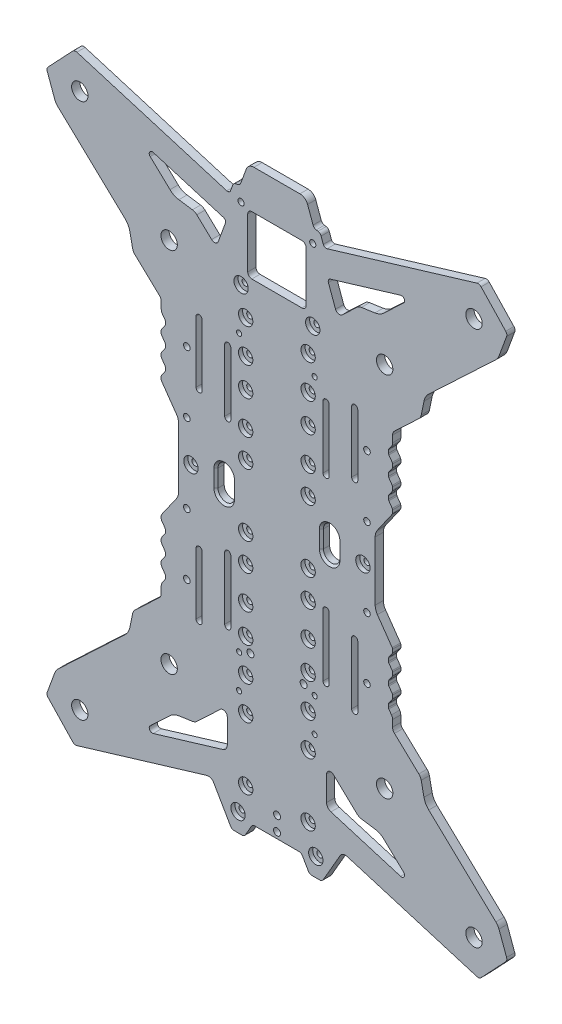
SolidWorks part; units mm, degrees
ref_plane "Front Plane" through (0, 0, 0) normal (0, 0, 1) x (1, 0, 0)
ref_plane "Top Plane" through (0, 0, 0) normal (0, 1, 0) x (1, 0, 0)
ref_plane "Right Plane" through (0, 0, 0) normal (1, 0, 0) x (0, 0, -1)
sketch "Model" plane through (0, 0, 0) normal (0, 0, 1) x (1, 0, 0)
  line L0 (183.8108, 197.417) -> (183.8108, 227.917)
  line L1 (186.8108, 227.917) -> (186.8108, 197.417)
  line L2 (138.8108, 139.917) -> (138.8108, 109.417)
  line L3 (135.8108, 109.417) -> (135.8108, 139.917)
  line L4 (186.8108, 139.917) -> (186.8108, 109.417)
  line L5 (183.8108, 109.417) -> (183.8108, 139.917)
  line L6 (135.8108, 197.417) -> (135.8108, 227.917)
  line L7 (138.8108, 227.917) -> (138.8108, 197.417)
  line L8 (147.0608, 264.0945) -> (147.0608, 288.5945)
  line L9 (173.5608, 262.0945) -> (149.0608, 262.0945)
  line L10 (175.5608, 288.5945) -> (175.5608, 264.0945)
  line L11 (149.0608, 290.5945) -> (173.5608, 290.5945)
  line L12 (133.6884, 72.3677) -> (122.1935, 61.5247)
  line L13 (120.0282, 60.4766) -> (113.4215, 59.5095)
  line L14 (100.8847, 45.7661) -> (134.926, 56.02)
  line L15 (209.2, 59.5095) -> (202.5933, 60.4766)
  line L16 (200.428, 61.5247) -> (188.9331, 72.3677)
  line L17 (185.5608, 58.8925) -> (185.5608, 70.9128)
  line L18 (187.6955, 56.02) -> (221.7368, 45.7661)
  line L19 (223.1987, 48.2935) -> (213.5306, 57.4133)
  line L20 (113.4215, 277.8244) -> (120.0282, 276.8573)
  line L21 (122.1935, 275.8092) -> (129.4288, 268.9842)
  line L22 (135.174, 281.2392) -> (100.8847, 291.5678)
  line L23 (99.4228, 289.0404) -> (109.0909, 279.9206)
  line L24 (261.0344, 314.783) -> (273.0616, 302.0327)
  line L25 (273.4849, 299.9728) -> (269.7846, 289.8648)
  line L26 (268.2674, 287.5628) -> (235.4884, 256.6428)
  line L27 (233.1432, 252.4417) -> (231.7925, 245.9027)
  line L28 (230.6199, 243.8022) -> (218.7522, 232.6075)
  line L29 (217.8108, 230.4252) -> (217.8108, 227.2161)
  line L30 (217.2682, 225.4954) -> (215.9916, 223.6722)
  line L31 (215.8108, 223.0986) -> (215.8108, 221.7292)
  line L32 (215.9916, 221.1557) -> (217.6299, 218.8159)
  line L33 (217.8108, 218.2423) -> (217.8108, 216.8729)
  line L34 (217.6299, 216.2994) -> (215.9916, 213.9596)
  line L35 (215.8108, 213.386) -> (215.8108, 212.0166)
  line L36 (215.9916, 211.4431) -> (217.6299, 209.1033)
  line L37 (217.8108, 208.5298) -> (217.8108, 207.1603)
  line L38 (217.6299, 206.5868) -> (215.9916, 204.247)
  line L39 (215.8108, 203.6735) -> (215.8108, 202.304)
  line L40 (215.9916, 201.7305) -> (217.6299, 199.3907)
  line L41 (217.8108, 198.8172) -> (217.8108, 197.4478)
  line L42 (217.6299, 196.8742) -> (210.3959, 186.5429)
  line L43 (209.3108, 183.1014) -> (209.3108, 154.2325)
  line L44 (210.3959, 150.791) -> (217.6299, 140.4597)
  line L45 (217.8108, 139.8861) -> (217.8108, 138.5167)
  line L46 (217.6299, 137.9432) -> (215.9916, 135.6034)
  line L47 (215.8108, 135.0299) -> (215.8108, 133.6605)
  line L48 (215.9916, 133.0869) -> (217.6299, 130.7471)
  line L49 (217.8108, 130.1736) -> (217.8108, 128.8042)
  line L50 (217.6299, 128.2306) -> (215.9916, 125.8908)
  line L51 (215.8108, 125.3173) -> (215.8108, 123.9479)
  line L52 (215.9916, 123.3743) -> (217.6299, 121.0345)
  line L53 (217.8108, 120.461) -> (217.8108, 119.0916)
  line L54 (217.6299, 118.518) -> (215.9916, 116.1782)
  line L55 (215.8108, 115.6047) -> (215.8108, 114.2353)
  line L56 (215.9916, 113.6617) -> (217.2682, 111.8385)
  line L57 (217.8108, 110.1178) -> (217.8108, 106.9087)
  line L58 (218.7522, 104.7264) -> (230.6199, 93.5317)
  line L59 (231.7925, 91.4312) -> (233.1432, 84.8922)
  line L60 (235.4884, 80.6911) -> (268.2674, 49.7711)
  line L61 (269.7846, 47.4691) -> (273.4849, 37.3611)
  line L62 (273.0616, 35.3012) -> (261.0344, 22.5509)
  line L63 (259.0027, 22.0083) -> (195.64, 41.0944)
  line L64 (192.1766, 39.7219) -> (183.942, 25.4591)
  line L65 (182.2099, 24.4591) -> (178.4116, 24.4591)
  line L66 (176.6796, 25.4591) -> (173.7928, 30.4591)
  line L67 (172.0608, 31.4591) -> (150.5608, 31.4591)
  line L68 (148.8287, 30.4591) -> (145.942, 25.4591)
  line L69 (144.2099, 24.4591) -> (140.4116, 24.4591)
  line L70 (138.6796, 25.4591) -> (130.4449, 39.7219)
  line L71 (126.9816, 41.0944) -> (63.6188, 22.0083)
  line L72 (61.5871, 22.5509) -> (49.5599, 35.3012)
  line L73 (49.1366, 37.3611) -> (52.8369, 47.4691)
  line L74 (54.3542, 49.7711) -> (87.1331, 80.6911)
  line L75 (89.4783, 84.8922) -> (90.8291, 91.4312)
  line L76 (92.0016, 93.5317) -> (103.8693, 104.7264)
  line L77 (104.8108, 106.9087) -> (104.8108, 110.1178)
  line L78 (105.3533, 111.8385) -> (106.6299, 113.6617)
  line L79 (106.8108, 114.2353) -> (106.8108, 115.6047)
  line L80 (106.6299, 116.1782) -> (104.9916, 118.518)
  line L81 (104.8108, 119.0916) -> (104.8108, 120.461)
  line L82 (104.9916, 121.0345) -> (106.6299, 123.3743)
  line L83 (106.6299, 125.8908) -> (104.9916, 128.2306)
  line L84 (104.8108, 128.8042) -> (104.8108, 130.1736)
  line L85 (104.9916, 130.7471) -> (106.6299, 133.0869)
  line L86 (106.8108, 133.6605) -> (106.8108, 135.0299)
  line L87 (106.6299, 135.6034) -> (104.9916, 137.9432)
  line L88 (104.8108, 138.5167) -> (104.8108, 139.8861)
  line L89 (104.9916, 140.4597) -> (112.2257, 150.791)
  line L90 (113.3108, 154.2325) -> (113.3108, 183.1014)
  line L91 (112.2257, 186.5429) -> (104.9916, 196.8742)
  line L92 (104.8108, 197.4478) -> (104.8108, 198.8172)
  line L93 (104.9916, 199.3907) -> (106.6299, 201.7305)
  line L94 (106.8108, 202.304) -> (106.8108, 203.6735)
  line L95 (106.6299, 204.247) -> (104.9916, 206.5868)
  line L96 (104.8108, 207.1603) -> (104.8108, 208.5298)
  line L97 (104.9916, 209.1033) -> (106.6299, 211.4431)
  line L98 (106.8108, 212.0166) -> (106.8108, 213.386)
  line L99 (106.6299, 213.9596) -> (104.9916, 216.2994)
  line L100 (104.8108, 216.8729) -> (104.8108, 218.2423)
  line L101 (104.9916, 218.8159) -> (106.6299, 221.1557)
  line L102 (106.8108, 221.7292) -> (106.8108, 223.0986)
  line L103 (106.6299, 223.6722) -> (105.3533, 225.4954)
  line L104 (104.8108, 227.2161) -> (104.8108, 230.4252)
  line L105 (103.8693, 232.6075) -> (92.0016, 243.8022)
  line L106 (90.8291, 245.9027) -> (89.4783, 252.4417)
  line L107 (87.1331, 256.6428) -> (54.3542, 287.5628)
  line L108 (52.8369, 289.8648) -> (49.1366, 299.9728)
  line L109 (49.5599, 302.0327) -> (61.5871, 314.783)
  line L110 (63.6188, 315.3256) -> (136.8099, 293.279)
  line L111 (138.6521, 294.2022) -> (139.728, 297.1583)
  line L112 (141.2601, 298.4439) -> (142.113, 298.5943)
  line L113 (143.6451, 299.8798) -> (146.325, 307.2429)
  line L114 (150.0838, 309.8748) -> (172.5378, 309.8748)
  line L115 (176.2965, 307.2429) -> (178.9765, 299.8798)
  line L116 (180.5086, 298.5943) -> (181.3614, 298.4439)
  line L117 (185.8116, 293.279) -> (259.0027, 315.3256)
  line L118 (193.1927, 268.9842) -> (200.428, 275.8092)
  line L119 (202.5933, 276.8573) -> (209.2, 277.8244)
  line L120 (221.7368, 291.5678) -> (187.4475, 281.2392)
  line L121 (186.4706, 279.2899) -> (189.941, 269.7551)
  line L122 (106.8108, 123.9479) -> (106.8108, 125.3173)
  line L123 (137.0608, 70.9128) -> (137.0608, 58.8925)
  line L124 (109.0909, 57.4133) -> (99.4228, 48.2935)
  line L125 (132.6805, 269.7551) -> (136.1509, 279.2899)
  line L126 (182.8935, 297.1583) -> (183.9694, 294.2022)
  line L127 (213.5306, 279.9206) -> (223.1987, 289.0404)
  circle A0 centre (178.8108, 292.022) radius 1.5
  arc A1 (183.8108, 197.417) -> (186.8108, 197.417) centre (185.3108, 197.417) ccw
  arc A2 (186.8108, 227.917) -> (183.8108, 227.917) centre (185.3108, 227.917) ccw
  arc A3 (138.8108, 139.917) -> (135.8108, 139.917) centre (137.3108, 139.917) ccw
  arc A4 (135.8108, 109.417) -> (138.8108, 109.417) centre (137.3108, 109.417) ccw
  circle A5 centre (213.9455, 258.3167) radius 4
  circle A6 centre (257.5914, 299.4875) radius 4
  circle A7 centre (65.0301, 299.4875) radius 4
  circle A8 centre (108.6761, 258.3167) radius 4
  circle A9 centre (108.6761, 79.0172) radius 4
  circle A10 centre (65.0301, 37.8464) radius 4
  circle A11 centre (257.5914, 37.8464) radius 4
  circle A12 centre (213.9455, 79.0172) radius 4
  arc A13 (186.8108, 139.917) -> (183.8108, 139.917) centre (185.3108, 139.917) ccw
  arc A14 (183.8108, 109.417) -> (186.8108, 109.417) centre (185.3108, 109.417) ccw
  arc A15 (135.8108, 197.417) -> (138.8108, 197.417) centre (137.3108, 197.417) ccw
  arc A16 (138.8108, 227.917) -> (135.8108, 227.917) centre (137.3108, 227.917) ccw
  circle A17 centre (143.8108, 292.022) radius 1.5
  arc A18 (147.0608, 264.0945) -> (149.0608, 262.0945) centre (149.0608, 264.0945) ccw
  arc A19 (173.5608, 262.0945) -> (175.5608, 264.0945) centre (173.5608, 264.0945) ccw
  arc A20 (175.5608, 288.5945) -> (173.5608, 290.5945) centre (173.5608, 288.5945) ccw
  arc A21 (149.0608, 290.5945) -> (147.0608, 288.5945) centre (149.0608, 288.5945) ccw
  circle A22 centre (146.0608, 227.917) radius 3.5 construction
  circle A23 centre (176.5608, 227.917) radius 3.5 construction
  circle A24 centre (176.5608, 197.417) radius 3.5 construction
  circle A25 centre (146.0608, 197.417) radius 3.5 construction
  circle A26 centre (119.3108, 168.667) radius 3.5 construction
  circle A27 centre (203.3108, 168.667) radius 3.5 construction
  circle A28 centre (146.0608, 183.917) radius 3.5 construction
  circle A29 centre (176.5608, 183.917) radius 3.5 construction
  circle A30 centre (146.0608, 153.417) radius 3.5 construction
  circle A31 centre (176.5608, 153.417) radius 3.5 construction
  circle A32 centre (146.0608, 139.917) radius 3.5 construction
  circle A33 centre (176.5608, 139.917) radius 3.5 construction
  circle A34 centre (146.0608, 109.417) radius 3.5 construction
  circle A35 centre (176.5608, 109.417) radius 3.5 construction
  circle A36 centre (146.0608, 76.667) radius 3.5 construction
  circle A37 centre (176.5608, 76.667) radius 3.5 construction
  circle A38 centre (146.0608, 46.167) radius 3.5 construction
  circle A39 centre (176.5608, 46.167) radius 3.5 construction
  circle A40 centre (142.3108, 33.4591) radius 3.5 construction
  circle A41 centre (180.3108, 33.4591) radius 3.5 construction
  circle A42 centre (176.5608, 93.042) radius 3.5 construction
  circle A43 centre (146.0608, 93.042) radius 3.5 construction
  circle A44 centre (176.5608, 123.542) radius 3.5 construction
  circle A45 centre (146.0608, 123.542) radius 3.5 construction
  circle A46 centre (176.5608, 213.792) radius 3.5 construction
  circle A47 centre (146.0608, 213.792) radius 3.5 construction
  circle A48 centre (176.5608, 244.292) radius 3.5 construction
  circle A49 centre (146.0608, 244.292) radius 3.5 construction
  circle A50 centre (178.8108, 257.022) radius 3.5 construction
  circle A51 centre (143.8108, 257.022) radius 3.5 construction
  arc A52 (137.0608, 70.9128) -> (133.6884, 72.3677) centre (135.0608, 70.9128) ccw
  arc A53 (120.0282, 60.4766) -> (122.1935, 61.5247) centre (119.4488, 64.4344) ccw
  arc A54 (113.4215, 59.5095) -> (109.0909, 57.4133) centre (114.5803, 51.5938) ccw
  arc A55 (99.4228, 48.2935) -> (100.8847, 45.7661) centre (100.4521, 47.2023) ccw
  arc A56 (134.926, 56.02) -> (137.0608, 58.8925) centre (134.0608, 58.8925) ccw
  arc A57 (200.428, 61.5247) -> (202.5933, 60.4766) centre (203.1727, 64.4344) ccw
  arc A58 (188.9331, 72.3677) -> (185.5608, 70.9128) centre (187.5608, 70.9128) ccw
  arc A59 (185.5608, 58.8925) -> (187.6955, 56.02) centre (188.5608, 58.8925) ccw
  arc A60 (221.7368, 45.7661) -> (223.1987, 48.2935) centre (222.1695, 47.2023) ccw
  arc A61 (213.5306, 57.4133) -> (209.2, 59.5095) centre (208.0412, 51.5938) ccw
  arc A62 (122.1935, 275.8092) -> (120.0282, 276.8573) centre (119.4488, 272.8995) ccw
  arc A63 (129.4288, 268.9842) -> (132.6805, 269.7551) centre (130.8012, 270.4391) ccw
  arc A64 (136.1509, 279.2899) -> (135.174, 281.2392) centre (134.7414, 279.8029) ccw
  arc A65 (100.8847, 291.5678) -> (99.4228, 289.0404) centre (100.4521, 290.1316) ccw
  arc A66 (109.0909, 279.9206) -> (113.4215, 277.8244) centre (114.5803, 285.7401) ccw
  arc A67 (261.0344, 314.783) -> (259.0027, 315.3256) centre (259.5795, 313.4106) ccw
  arc A68 (273.4849, 299.9728) -> (273.0616, 302.0327) centre (271.6068, 300.6603) ccw
  arc A69 (268.2674, 287.5628) -> (269.7846, 289.8648) centre (264.1503, 291.9274) ccw
  arc A70 (235.4884, 256.6428) -> (233.1432, 252.4417) centre (240.9778, 250.8233) ccw
  arc A71 (230.6199, 243.8022) -> (231.7925, 245.9027) centre (227.8752, 246.7119) ccw
  arc A72 (218.7522, 232.6075) -> (217.8108, 230.4252) centre (220.8108, 230.4252) ccw
  arc A73 (217.2682, 225.4954) -> (217.8108, 227.2161) centre (214.8108, 227.2161) ccw
  arc A74 (215.9916, 223.6722) -> (215.8108, 223.0986) centre (216.8108, 223.0986) ccw
  arc A75 (215.8108, 221.7292) -> (215.9916, 221.1557) centre (216.8108, 221.7292) ccw
  arc A76 (217.8108, 218.2423) -> (217.6299, 218.8159) centre (216.8108, 218.2423) ccw
  arc A77 (217.6299, 216.2994) -> (217.8108, 216.8729) centre (216.8108, 216.8729) ccw
  arc A78 (215.9916, 213.9596) -> (215.8108, 213.386) centre (216.8108, 213.386) ccw
  arc A79 (215.8108, 212.0166) -> (215.9916, 211.4431) centre (216.8108, 212.0166) ccw
  arc A80 (217.8108, 208.5298) -> (217.6299, 209.1033) centre (216.8108, 208.5298) ccw
  arc A81 (217.6299, 206.5868) -> (217.8108, 207.1603) centre (216.8108, 207.1603) ccw
  arc A82 (215.9916, 204.247) -> (215.8108, 203.6735) centre (216.8108, 203.6735) ccw
  arc A83 (215.8108, 202.304) -> (215.9916, 201.7305) centre (216.8108, 202.3041) ccw
  arc A84 (217.8108, 198.8172) -> (217.6299, 199.3907) centre (216.8108, 198.8172) ccw
  arc A85 (217.6299, 196.8742) -> (217.8108, 197.4478) centre (216.8108, 197.4478) ccw
  arc A86 (210.3959, 186.5429) -> (209.3108, 183.1014) centre (215.3108, 183.1014) ccw
  arc A87 (209.3108, 154.2325) -> (210.3959, 150.791) centre (215.3108, 154.2325) ccw
  arc A88 (217.8108, 139.8861) -> (217.6299, 140.4597) centre (216.8108, 139.8861) ccw
  arc A89 (217.6299, 137.9432) -> (217.8108, 138.5167) centre (216.8108, 138.5167) ccw
  arc A90 (215.9916, 135.6034) -> (215.8108, 135.0299) centre (216.8108, 135.0299) ccw
  arc A91 (215.8108, 133.6605) -> (215.9916, 133.0869) centre (216.8108, 133.6604) ccw
  arc A92 (217.8108, 130.1736) -> (217.6299, 130.7471) centre (216.8108, 130.1736) ccw
  arc A93 (217.6299, 128.2306) -> (217.8108, 128.8042) centre (216.8108, 128.8042) ccw
  arc A94 (215.9916, 125.8908) -> (215.8108, 125.3173) centre (216.8108, 125.3173) ccw
  arc A95 (215.8108, 123.9479) -> (215.9916, 123.3743) centre (216.8108, 123.9479) ccw
  arc A96 (217.8108, 120.461) -> (217.6299, 121.0345) centre (216.8108, 120.461) ccw
  arc A97 (217.6299, 118.518) -> (217.8108, 119.0916) centre (216.8108, 119.0916) ccw
  arc A98 (215.9916, 116.1782) -> (215.8108, 115.6047) centre (216.8108, 115.6047) ccw
  arc A99 (215.8108, 114.2353) -> (215.9916, 113.6617) centre (216.8108, 114.2353) ccw
  arc A100 (217.8108, 110.1178) -> (217.2682, 111.8385) centre (214.8108, 110.1178) ccw
  arc A101 (217.8108, 106.9087) -> (218.7522, 104.7264) centre (220.8108, 106.9087) ccw
  arc A102 (231.7925, 91.4312) -> (230.6199, 93.5317) centre (227.8752, 90.622) ccw
  arc A103 (233.1432, 84.8922) -> (235.4884, 80.6911) centre (240.9778, 86.5106) ccw
  arc A104 (269.7846, 47.4691) -> (268.2674, 49.7711) centre (264.1503, 45.4065) ccw
  arc A105 (273.0616, 35.3012) -> (273.4849, 37.3611) centre (271.6068, 36.6736) ccw
  arc A106 (259.0027, 22.0083) -> (261.0344, 22.5509) centre (259.5795, 23.9233) ccw
  arc A107 (195.64, 41.0944) -> (192.1766, 39.7219) centre (194.7747, 38.2219) ccw
  arc A108 (182.2099, 24.4591) -> (183.942, 25.4591) centre (182.2099, 26.4591) ccw
  arc A109 (176.6796, 25.4591) -> (178.4116, 24.4591) centre (178.4116, 26.4591) ccw
  arc A110 (173.7928, 30.4591) -> (172.0608, 31.4591) centre (172.0608, 29.4591) ccw
  arc A111 (150.5608, 31.4591) -> (148.8287, 30.4591) centre (150.5608, 29.4591) ccw
  arc A112 (144.2099, 24.4591) -> (145.942, 25.4591) centre (144.2099, 26.4591) ccw
  arc A113 (138.6796, 25.4591) -> (140.4116, 24.4591) centre (140.4116, 26.4591) ccw
  arc A114 (130.4449, 39.7219) -> (126.9816, 41.0944) centre (127.8468, 38.2219) ccw
  arc A115 (61.5871, 22.5509) -> (63.6188, 22.0083) centre (63.042, 23.9233) ccw
  arc A116 (49.1366, 37.3611) -> (49.5599, 35.3012) centre (51.0147, 36.6736) ccw
  arc A117 (54.3542, 49.7711) -> (52.8369, 47.4691) centre (58.4712, 45.4065) ccw
  arc A118 (87.1331, 80.6911) -> (89.4783, 84.8922) centre (81.6437, 86.5106) ccw
  arc A119 (92.0016, 93.5317) -> (90.8291, 91.4312) centre (94.7464, 90.622) ccw
  arc A120 (103.8693, 104.7264) -> (104.8108, 106.9087) centre (101.8108, 106.9087) ccw
  arc A121 (105.3533, 111.8385) -> (104.8108, 110.1178) centre (107.8108, 110.1178) ccw
  arc A122 (106.6299, 113.6617) -> (106.8108, 114.2353) centre (105.8108, 114.2353) ccw
  arc A123 (106.8108, 115.6047) -> (106.6299, 116.1782) centre (105.8108, 115.6047) ccw
  arc A124 (104.8108, 119.0916) -> (104.9916, 118.518) centre (105.8108, 119.0916) ccw
  arc A125 (104.9916, 121.0345) -> (104.8108, 120.461) centre (105.8108, 120.461) ccw
  arc A126 (106.6299, 123.3743) -> (106.8108, 123.9479) centre (105.8108, 123.9479) ccw
  arc A127 (106.8108, 125.3173) -> (106.6299, 125.8908) centre (105.8108, 125.3173) ccw
  arc A128 (104.8108, 128.8042) -> (104.9916, 128.2306) centre (105.8108, 128.8042) ccw
  arc A129 (104.9916, 130.7471) -> (104.8108, 130.1736) centre (105.8108, 130.1736) ccw
  arc A130 (106.6299, 133.0869) -> (106.8108, 133.6605) centre (105.8108, 133.6604) ccw
  arc A131 (106.8108, 135.0299) -> (106.6299, 135.6034) centre (105.8108, 135.0299) ccw
  arc A132 (104.8108, 138.5167) -> (104.9916, 137.9432) centre (105.8108, 138.5167) ccw
  arc A133 (104.9916, 140.4597) -> (104.8108, 139.8861) centre (105.8108, 139.8861) ccw
  arc A134 (112.2257, 150.791) -> (113.3108, 154.2325) centre (107.3108, 154.2325) ccw
  arc A135 (113.3108, 183.1014) -> (112.2257, 186.5429) centre (107.3108, 183.1014) ccw
  arc A136 (104.8108, 197.4478) -> (104.9916, 196.8742) centre (105.8108, 197.4478) ccw
  arc A137 (104.9916, 199.3907) -> (104.8108, 198.8172) centre (105.8108, 198.8172) ccw
  arc A138 (106.6299, 201.7305) -> (106.8108, 202.304) centre (105.8108, 202.3041) ccw
  arc A139 (106.8108, 203.6735) -> (106.6299, 204.247) centre (105.8108, 203.6735) ccw
  arc A140 (104.8108, 207.1603) -> (104.9916, 206.5868) centre (105.8108, 207.1603) ccw
  arc A141 (104.9916, 209.1033) -> (104.8108, 208.5298) centre (105.8108, 208.5298) ccw
  arc A142 (106.6299, 211.4431) -> (106.8108, 212.0166) centre (105.8108, 212.0166) ccw
  arc A143 (106.8108, 213.386) -> (106.6299, 213.9596) centre (105.8108, 213.386) ccw
  arc A144 (104.8108, 216.8729) -> (104.9916, 216.2994) centre (105.8108, 216.8729) ccw
  arc A145 (104.9916, 218.8159) -> (104.8108, 218.2423) centre (105.8108, 218.2423) ccw
  arc A146 (106.6299, 221.1557) -> (106.8108, 221.7292) centre (105.8108, 221.7292) ccw
  arc A147 (106.8108, 223.0986) -> (106.6299, 223.6722) centre (105.8108, 223.0986) ccw
  arc A148 (104.8108, 227.2161) -> (105.3533, 225.4954) centre (107.8108, 227.2161) ccw
  arc A149 (104.8108, 230.4252) -> (103.8693, 232.6075) centre (101.8108, 230.4252) ccw
  arc A150 (90.8291, 245.9027) -> (92.0016, 243.8022) centre (94.7464, 246.7119) ccw
  arc A151 (89.4783, 252.4417) -> (87.1331, 256.6428) centre (81.6437, 250.8233) ccw
  arc A152 (52.8369, 289.8648) -> (54.3542, 287.5628) centre (58.4712, 291.9274) ccw
  arc A153 (49.5599, 302.0327) -> (49.1366, 299.9728) centre (51.0147, 300.6603) ccw
  arc A154 (63.6188, 315.3256) -> (61.5871, 314.783) centre (63.042, 313.4106) ccw
  arc A155 (136.8099, 293.279) -> (138.6521, 294.2022) centre (137.2425, 294.7152) ccw
  arc A156 (141.2601, 298.4439) -> (139.728, 297.1583) centre (141.6074, 296.4743) ccw
  arc A157 (142.113, 298.5943) -> (143.6451, 299.8798) centre (141.7657, 300.5639) ccw
  arc A158 (150.0838, 309.8748) -> (146.325, 307.2429) centre (150.0838, 305.8748) ccw
  arc A159 (176.2965, 307.2429) -> (172.5378, 309.8748) centre (172.5378, 305.8748) ccw
  arc A160 (178.9765, 299.8798) -> (180.5086, 298.5943) centre (180.8559, 300.5639) ccw
  arc A161 (182.8935, 297.1583) -> (181.3614, 298.4439) centre (181.0141, 296.4743) ccw
  arc A162 (183.9694, 294.2022) -> (185.8116, 293.279) centre (185.379, 294.7152) ccw
  arc A163 (202.5933, 276.8573) -> (200.428, 275.8092) centre (203.1727, 272.8995) ccw
  arc A164 (209.2, 277.8244) -> (213.5306, 279.9206) centre (208.0412, 285.7401) ccw
  arc A165 (223.1987, 289.0404) -> (221.7368, 291.5678) centre (222.1695, 290.1316) ccw
  arc A166 (187.4475, 281.2392) -> (186.4706, 279.2899) centre (187.8801, 279.8029) ccw
  arc A167 (189.941, 269.7551) -> (193.1927, 268.9842) centre (191.8204, 270.4391) ccw
  circle A168 centre (176.5608, 227.917) radius 1.5
  circle A169 centre (146.0608, 227.917) radius 1.5
  circle A170 centre (146.0608, 123.542) radius 1.5
  circle A171 centre (176.5608, 123.542) radius 1.5
  circle A172 centre (146.0608, 93.042) radius 1.5
  circle A173 centre (176.5608, 93.042) radius 1.5
  circle A174 centre (180.3108, 33.4591) radius 1.5
  circle A175 centre (142.3108, 33.4591) radius 1.5
  circle A176 centre (176.5608, 76.667) radius 1.5
  circle A177 centre (146.0608, 76.667) radius 1.5
  circle A178 centre (146.0608, 109.417) radius 1.5
  circle A179 centre (119.3108, 168.667) radius 1.5
  circle A180 centre (176.5608, 139.917) radius 1.5
  circle A181 centre (146.0608, 139.917) radius 1.5
  circle A182 centre (146.0608, 213.792) radius 1.5
  circle A183 centre (176.5608, 213.792) radius 1.5
  circle A184 centre (176.5608, 109.417) radius 1.5
  circle A185 centre (176.5608, 197.417) radius 1.5
  circle A186 centre (176.5608, 244.292) radius 1.5
  circle A187 centre (203.3108, 168.667) radius 1.5
  circle A188 centre (143.8108, 257.022) radius 1.5
  circle A189 centre (178.8108, 257.022) radius 1.5
  circle A190 centre (146.0608, 244.292) radius 1.5
  circle A191 centre (146.0608, 46.167) radius 1.5
  circle A192 centre (146.0608, 197.417) radius 1.5
  circle A193 centre (176.5608, 46.167) radius 1.5
  circle A194 centre (146.0608, 183.917) radius 1.5
  circle A195 centre (146.0608, 153.417) radius 1.5
  circle A196 centre (176.5608, 153.417) radius 1.5
  circle A197 centre (176.5608, 183.917) radius 1.5
extrude "Main Body" add sketch "Model" along normal blind 4
sketch "Sketch2" plane through (0, 0, 4) normal (0, 0, 1) x (1, 0, 0)
  circle A0 centre (176.5608, 46.167) radius 3.5 construction
  circle A1 centre (180.3108, 33.4591) radius 3.5 construction
  circle A2 centre (142.3108, 33.4591) radius 3.5 construction
  circle A3 centre (146.0608, 46.167) radius 3.5 construction
  circle A4 centre (176.5608, 76.667) radius 3.5 construction
  circle A5 centre (146.0608, 76.667) radius 3.5 construction
  circle A6 centre (146.0608, 93.042) radius 3.5 construction
  circle A7 centre (176.5608, 93.042) radius 3.5 construction
  circle A8 centre (176.5608, 109.417) radius 3.5 construction
  circle A9 centre (146.0608, 109.417) radius 3.5 construction
  circle A10 centre (176.5608, 123.542) radius 3.5 construction
  circle A11 centre (146.0608, 123.542) radius 3.5 construction
  circle A12 centre (146.0608, 139.917) radius 3.5 construction
  circle A13 centre (176.5608, 139.917) radius 3.5 construction
  circle A14 centre (176.5608, 139.917) radius 1.5 construction
  circle A15 centre (203.3108, 168.667) radius 3.5 construction
  circle A16 centre (176.5608, 153.417) radius 3.5 construction
  circle A17 centre (146.0608, 153.417) radius 3.5 construction
  circle A18 centre (119.3108, 168.667) radius 3.5 construction
  circle A19 centre (146.0608, 183.917) radius 3.5 construction
  circle A20 centre (176.5608, 183.917) radius 3.5 construction
  circle A21 centre (176.5608, 197.417) radius 3.5 construction
  circle A22 centre (146.0608, 197.417) radius 3.5 construction
  circle A23 centre (176.5608, 213.792) radius 3.5 construction
  circle A24 centre (146.0608, 213.792) radius 3.5 construction
  circle A25 centre (146.0608, 227.917) radius 3.5 construction
  circle A26 centre (176.5608, 227.917) radius 3.5 construction
  circle A27 centre (176.5608, 244.292) radius 3.5 construction
  circle A28 centre (178.8108, 257.022) radius 3.5 construction
  circle A29 centre (146.0608, 244.292) radius 3.5 construction
  circle A30 centre (143.8108, 257.022) radius 3.5 construction
  circle A31 centre (176.5608, 46.167) radius 3.5
  circle A32 centre (180.3108, 33.4591) radius 3.5
  circle A33 centre (142.3108, 33.4591) radius 3.5
  circle A34 centre (146.0608, 46.167) radius 3.5
  circle A35 centre (176.5608, 76.667) radius 3.5
  circle A36 centre (146.0608, 76.667) radius 3.5
  circle A37 centre (146.0608, 93.042) radius 3.5
  circle A38 centre (176.5608, 93.042) radius 3.5
  circle A39 centre (176.5608, 109.417) radius 3.5
  circle A40 centre (146.0608, 109.417) radius 3.5
  circle A41 centre (176.5608, 123.542) radius 3.5
  circle A42 centre (146.0608, 123.542) radius 3.5
  circle A43 centre (146.0608, 139.917) radius 3.5
  circle A44 centre (176.5608, 139.917) radius 3.5
  circle A45 centre (176.5608, 139.917) radius 1.5
  circle A46 centre (203.3108, 168.667) radius 3.5
  circle A47 centre (176.5608, 153.417) radius 3.5
  circle A48 centre (146.0608, 153.417) radius 3.5
  circle A49 centre (119.3108, 168.667) radius 3.5
  circle A50 centre (146.0608, 183.917) radius 3.5
  circle A51 centre (176.5608, 183.917) radius 3.5
  circle A52 centre (176.5608, 197.417) radius 3.5
  circle A53 centre (146.0608, 197.417) radius 3.5
  circle A54 centre (176.5608, 213.792) radius 3.5
  circle A55 centre (146.0608, 213.792) radius 3.5
  circle A56 centre (146.0608, 227.917) radius 3.5
  circle A57 centre (176.5608, 227.917) radius 3.5
  circle A58 centre (176.5608, 244.292) radius 3.5
  circle A59 centre (178.8108, 257.022) radius 3.5
  circle A60 centre (146.0608, 244.292) radius 3.5
  circle A61 centre (143.8108, 257.022) radius 3.5
extrude "  Lower Fixture Point Countersink" cut sketch "Sketch2" against normal blind 2
sketch "Sketch3" plane through (0, 0, 0) normal (0, 0, -1) x (-1, 0, 0)
  line L0 (-124.8107, 134.6669) -> (-124.8107, 104.6669) construction
  line L1 (-121.8107, 104.6669) -> (-121.8107, 134.6669) construction
  line L2 (-124.8108, 232.6669) -> (-124.8107, 202.6669) construction
  line L3 (-121.8107, 202.6669) -> (-121.8107, 232.6669) construction
  line L4 (-200.8108, 232.6669) -> (-200.8107, 202.6669) construction
  line L5 (-197.8107, 202.6669) -> (-197.8107, 232.6669) construction
  line L6 (-197.8107, 104.6669) -> (-197.8107, 134.6669) construction
  line L7 (-200.8107, 134.6669) -> (-200.8107, 104.6669) construction
  line L8 (-124.8107, 134.6669) -> (-124.8107, 104.6669)
  line L9 (-121.8107, 104.6669) -> (-121.8107, 134.6669)
  line L10 (-124.8108, 232.6669) -> (-124.8107, 202.6669)
  line L11 (-121.8107, 202.6669) -> (-121.8107, 232.6669)
  line L12 (-200.8108, 232.6669) -> (-200.8107, 202.6669)
  line L13 (-197.8107, 202.6669) -> (-197.8107, 232.6669)
  line L14 (-197.8107, 104.6669) -> (-197.8107, 134.6669)
  line L15 (-200.8107, 134.6669) -> (-200.8107, 104.6669)
  arc A0 (-124.8107, 104.6669) -> (-121.8107, 104.6669) centre (-123.3107, 104.6669) ccw construction
  arc A1 (-121.8107, 134.6669) -> (-124.8107, 134.6669) centre (-123.3107, 134.6669) ccw construction
  arc A2 (-124.8107, 202.6669) -> (-121.8107, 202.6669) centre (-123.3107, 202.6669) ccw construction
  arc A3 (-121.8107, 232.6669) -> (-124.8108, 232.6669) centre (-123.3107, 232.6669) ccw construction
  arc A4 (-197.8107, 232.6669) -> (-200.8108, 232.6669) centre (-199.3108, 232.6669) ccw construction
  arc A5 (-200.8107, 202.6669) -> (-197.8107, 202.6669) centre (-199.3107, 202.6669) ccw construction
  arc A6 (-200.8107, 104.6669) -> (-197.8107, 104.6669) centre (-199.3107, 104.6669) ccw construction
  arc A7 (-197.8107, 134.6669) -> (-200.8107, 134.6669) centre (-199.3107, 134.6669) ccw construction
  arc A8 (-124.8107, 104.6669) -> (-121.8107, 104.6669) centre (-123.3107, 104.6669) ccw
  arc A9 (-121.8107, 134.6669) -> (-124.8107, 134.6669) centre (-123.3107, 134.6669) ccw
  arc A10 (-124.8107, 202.6669) -> (-121.8107, 202.6669) centre (-123.3107, 202.6669) ccw
  arc A11 (-121.8107, 232.6669) -> (-124.8108, 232.6669) centre (-123.3107, 232.6669) ccw
  arc A12 (-197.8107, 232.6669) -> (-200.8108, 232.6669) centre (-199.3108, 232.6669) ccw
  arc A13 (-200.8107, 202.6669) -> (-197.8107, 202.6669) centre (-199.3107, 202.6669) ccw
  arc A14 (-200.8107, 104.6669) -> (-197.8107, 104.6669) centre (-199.3107, 104.6669) ccw
  arc A15 (-197.8107, 134.6669) -> (-200.8107, 134.6669) centre (-199.3107, 134.6669) ccw
extrude "Extra Battery Strap Fixtures" cut sketch "Sketch3" against normal up to next
sketch "Sketch4" plane through (0, 0, 0) normal (0, 0, -1) x (-1, 0, 0)
  line L0 (-187.0608, 164.417) -> (-187.0608, 172.917) construction
  line L1 (-191.0608, 164.417) -> (-191.0608, 172.917)
  line L2 (-183.0608, 164.417) -> (-183.0608, 172.917)
  line L3 (-135.5608, 172.917) -> (-135.5608, 164.417) construction
  line L4 (-131.5608, 172.917) -> (-131.5608, 164.417)
  line L5 (-139.5608, 172.917) -> (-139.5608, 164.417)
  circle A0 centre (-187.0608, 172.917) radius 1.6 construction
  circle A1 centre (-187.0608, 164.417) radius 1.6 construction
  circle A2 centre (-135.5608, 172.917) radius 1.6 construction
  circle A3 centre (-135.5608, 164.417) radius 1.6 construction
  circle A4 centre (-187.0608, 172.917) radius 1.6 construction
  circle A5 centre (-187.0608, 164.417) radius 1.6 construction
  circle A6 centre (-135.5608, 172.917) radius 1.6 construction
  circle A7 centre (-135.5608, 164.417) radius 1.6 construction
  arc A8 (-191.0608, 164.417) -> (-183.0608, 164.417) centre (-187.0608, 164.417) ccw
  arc A9 (-183.0608, 172.917) -> (-191.0608, 172.917) centre (-187.0608, 172.917) ccw
  arc A10 (-131.5608, 172.917) -> (-139.5608, 172.917) centre (-135.5608, 172.917) ccw
  arc A11 (-139.5608, 164.417) -> (-131.5608, 164.417) centre (-135.5608, 164.417) ccw
  point P12 (-187.0608, 168.667)
  point P17 (-135.5608, 168.667)
  dimension "D1" = 8
extrude "Battery Cable Ingress" cut sketch "Sketch4" against normal up to next
chamfer "Battery Cable Ingress Chamfer" distance 1 angle 45 4 edges at (131.5608, 168.667, 4) (139.5608, 168.667, 4) (183.0608, 168.667, 4) (191.0608, 168.667, 4)
sketch "Sketch5" plane through (0, 0, 0) normal (0, 0, -1) x (-1, 0, 0)
  line L0 (-161.3108, 262.0945) -> (-161.3108, 31.4591) construction
  line L1 (-149.0608, 262.0945) -> (-173.5608, 262.0945) construction
  line L2 (-150.5608, 31.4591) -> (-172.0608, 31.4591) construction
  line L3 (-146.0608, 109.417) -> (-146.0608, 93.042) construction
  line L4 (-146.0608, 93.042) -> (-146.0608, 76.667) construction
  line L5 (-179.7608, 101.2295) -> (-142.8608, 101.2295) construction
  line L6 (-179.7608, 84.8545) -> (-142.8608, 84.8545) construction
  line L7 (-179.7608, 236.1045) -> (-142.8608, 236.1045) construction
  line L8 (-146.0608, 244.292) -> (-146.0608, 227.917) construction
  circle A4 centre (-142.8608, 84.8545) radius 1.25
  circle A5 centre (-142.8608, 101.2295) radius 1.25
  circle A6 centre (-142.8608, 236.1045) radius 1.25
  circle A7 centre (-179.7608, 236.1045) radius 1.25
  circle A8 centre (-179.7608, 101.2295) radius 1.25
  circle A9 centre (-179.7608, 84.8545) radius 1.25
  point P24 (-146.0608, 84.8545)
  point P25 (-146.0608, 101.2295)
  point P30 (-146.0608, 236.1045)
  dimension "D1" = 2.5
  dimension "D2" = 36.9
  dimension "D3" = 36.9
  dimension "D4" = 36.9
extrude "Mauch PL200 Mounting Points" cut sketch "Sketch5" against normal up to next
sketch "Sketch6" plane through (0, 0, 0) normal (0, 0, -1) x (-1, 0, 0)
  circle A0 centre (-174.3688, 103.4113) radius 1.7 construction
  circle A1 centre (-148.3688, 103.4113) radius 1.7 construction
  circle A2 centre (-161.3688, 34.4113) radius 1.7 construction
  circle A3 centre (-161.3688, 41.4113) radius 2.25 construction
  circle A4 centre (-174.3688, 103.4113) radius 1.7
  circle A5 centre (-148.3688, 103.4113) radius 1.7
  circle A6 centre (-161.3688, 34.4113) radius 1.7
  circle A7 centre (-161.3688, 41.4113) radius 2.25 construction
  circle A8 centre (-161.3688, 41.4113) radius 1.7
  dimension "D1" = 3.4
extrude "RFD Carrier Mounting Points" cut sketch "Sketch6" against normal up to next
sketch "Sketch7" plane through (0, 0, 0) normal (0, 0, -1) x (-1, 0, 0)
  circle A0 centre (-205.3108, 217.6395) radius 1.6 construction
  circle A1 centre (-205.3108, 187.6395) radius 1.6 construction
  circle A2 centre (-205.3107, 149.1394) radius 1.6 construction
  circle A3 centre (-205.3107, 119.1394) radius 1.6 construction
  circle A4 centre (-117.3107, 119.1395) radius 1.6 construction
  circle A5 centre (-117.3108, 149.1395) radius 1.6 construction
  circle A6 centre (-117.3107, 187.6395) radius 1.6 construction
  circle A7 centre (-117.3107, 217.6395) radius 1.6 construction
  circle A8 centre (-205.3108, 217.6395) radius 1.6
  circle A9 centre (-205.3108, 187.6395) radius 1.6
  circle A10 centre (-205.3107, 149.1394) radius 1.6
  circle A11 centre (-205.3107, 119.1394) radius 1.6
  circle A12 centre (-117.3107, 119.1395) radius 1.6
  circle A13 centre (-117.3108, 149.1395) radius 1.6
  circle A14 centre (-117.3107, 187.6395) radius 1.6
  circle A15 centre (-117.3107, 217.6395) radius 1.6
extrude "ESC Carrier Fixtures Points" cut sketch "Sketch7" against normal up to next
